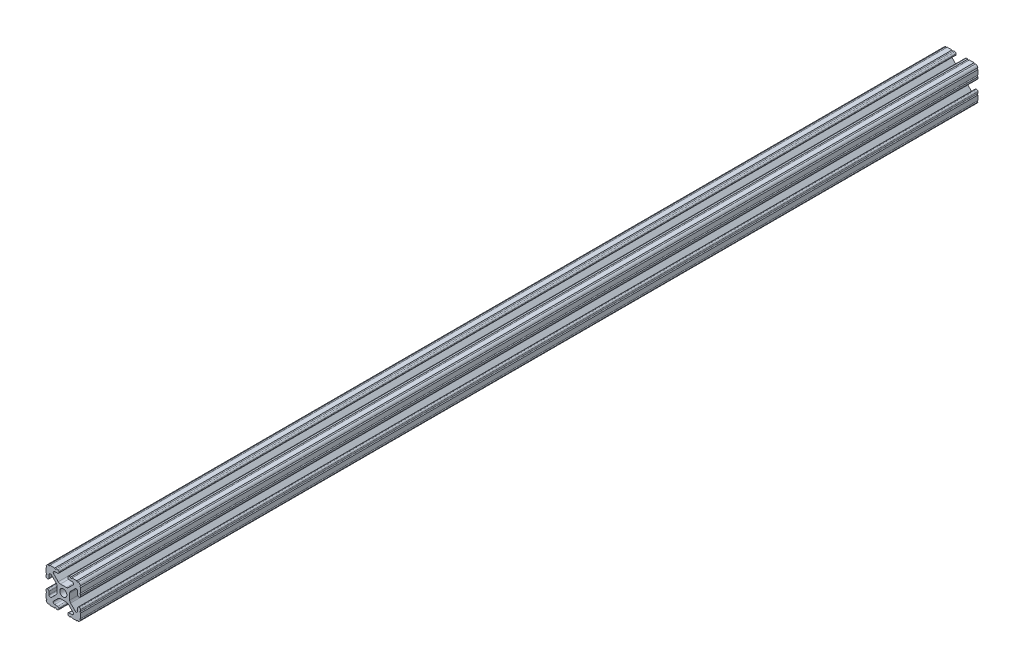
SolidWorks part; units mm, degrees
material "6061-T6 (SS)"
ref_plane "Front Plane" through (0, 0, 0) normal (0, 0, 1) x (1, 0, 0)
ref_plane "Top Plane" through (0, 0, 0) normal (0, 1, 0) x (1, 0, 0)
ref_plane "Right Plane" through (0, 0, 0) normal (1, 0, 0) x (0, 0, -1)
sketch "Sketch2" plane through (0, 0, 0) normal (0, 0, 1) x (1, 0, 0)
  line L0 (0, 12.7) -> (0, -12.7) construction
  line L1 (-12.7, 0) -> (12.7, 0) construction
  line L2 (3.2512, -12.7) -> (12.7, -12.7)
  line L3 (12.7, -12.7) -> (12.7, -3.2512)
  line L4 (3.2512, -12.7) -> (3.2512, -10.4902)
  line L5 (3.2512, -10.4902) -> (8.9276, -10.4902)
  line L6 (8.9276, -10.4902) -> (3.0856, -4.6482)
  line L7 (0, 0) -> (12.7, -12.7) construction
  line L8 (12.7, -3.2512) -> (10.4902, -3.2512)
  line L9 (10.4902, -3.2512) -> (10.4902, -8.9276)
  line L10 (10.4902, -8.9276) -> (4.6482, -3.0856)
  circle A0 centre (0, 0) radius 2.6035
  arc A1 (6.3485, -10.4902) -> (7.1039, -8.6665) centre (6.3485, -9.4219) ccw construction
  point P8 (0, -4.6482)
  dimension "Center Hole Diameter" = 5.207
  dimension "Rail Height" = 25.4
  dimension "Rail Width" = 25.4
  dimension "T-Slot Width" = 6.5024
  dimension "Slot Inner Width" = 14.8336
  dimension "Thickness" = 2.2098
  dimension "Slot Depth" = 5.842
  dimension "D1" = 2.2098
sketch "Sketch3" plane through (0, 0, 0) normal (1, 0, 0) x (0, 0, -1)
  line L0 (-328.6125, -12.7) -> (328.6125, -12.7) construction
  line L1 (-303.2125, 0) -> (303.2125, 0) construction
  dimension "Length" = 657.225
  dimension "D1" = 25.4
sketch "Sketch4" plane through (0, 0, 0) normal (0, 0, 1) x (1, 0, 0)
  line L0 (4.1904, -12.7) -> (10.1173, -12.7)
  line L1 (3.2512, -12.7) -> (12.7, -12.7) construction
  line L2 (3.2512, -12.7) -> (3.2512, -10.4902) construction
  line L3 (3.2512, -10.4902) -> (8.9276, -10.4902) construction
  line L4 (3.2512, -11.4294) -> (3.2512, -11.7608)
  line L5 (4.1904, -10.4902) -> (6.3485, -10.4902)
  line L6 (0, -4.6482) -> (2.164, -4.6482)
  line L7 (8.9276, -10.4902) -> (3.0856, -4.6482) construction
  line L8 (3.7373, -5.2999) -> (7.1039, -8.6665)
  line L9 (12.7, -12.7) -> (12.7, -3.2512) construction
  line L10 (10.4902, -8.9276) -> (4.6482, -3.0856) construction
  line L11 (10.4902, -3.2512) -> (10.4902, -8.9276) construction
  line L12 (10.4902, -6.3485) -> (10.4902, -4.1904)
  line L13 (12.7, -3.2512) -> (10.4902, -3.2512) construction
  line L14 (11.4294, -3.2512) -> (11.7608, -3.2512)
  line L15 (12.7, -4.1904) -> (12.7, -10.1173)
  line L16 (8.6665, -7.1039) -> (5.2999, -3.7373)
  line L17 (4.6482, 0) -> (4.6482, -2.164)
  line L18 (-12.7, 0) -> (12.7, 0) construction
  line L19 (0, -4.6482) -> (0, -2.6035)
  line L20 (0, 12.7) -> (0, -12.7) construction
  line L21 (4.6482, 0) -> (2.6035, 0)
  arc A0 (3.2512, -11.7608) -> (4.1904, -12.7) centre (4.1904, -11.7608) ccw
  arc A2 (3.2512, -11.4294) -> (4.1904, -10.4902) centre (4.1904, -11.4294) cw
  arc A3 (6.3485, -10.4902) -> (7.1039, -8.6665) centre (6.3485, -9.4219) ccw
  arc A4 (2.164, -4.6482) -> (3.7373, -5.2999) centre (2.164, -6.8732) cw
  arc A5 (10.1173, -12.7) -> (12.7, -10.1173) centre (10.1173, -10.1173) ccw
  arc A6 (8.6665, -7.1039) -> (10.4902, -6.3485) centre (9.4219, -6.3485) ccw
  arc A7 (10.4902, -4.1904) -> (11.4294, -3.2512) centre (11.4294, -4.1904) cw
  arc A8 (11.7608, -3.2512) -> (12.7, -4.1904) centre (11.7608, -4.1904) cw
  arc A9 (5.2999, -3.7373) -> (4.6482, -2.164) centre (6.8732, -2.164) cw
  circle A10 centre (0, 0) radius 2.6035 construction
  arc A11 (0, -2.6035) -> (2.6035, 0) centre (0, 0) ccw
  dimension "D1" = 2.5827
  dimension "D2" = 2.225
  dimension "D3" = 0.9392
extrude "Boss-Extrude1" add sketch "Sketch4" along normal mid plane 657.225
sketch "Sketch5" plane through (0, 0, 0) normal (0, 0, 1) x (1, 0, 0)
  line L0 (3.2512, -12.7) -> (12.7, -12.7) construction
  line L1 (4.1904, -10.4902) -> (6.3485, -10.4902) construction
  line L3 (0, 0) -> (12.7, -12.7) construction
  line L4 (6.3485, -10.4902) -> (6.3485, -12.7) construction
  line L5 (8.9276, -10.4902) -> (3.0856, -4.6482) construction
  circle A0 centre (10.3562, -12.7) radius 0.5524
  circle A1 centre (5.796, -12.7) radius 0.5524
  circle A2 centre (12.7, -10.3562) radius 0.5524
  circle A3 centre (12.7, -5.796) radius 0.5524
  point P10 (5.2694, -10.4902)
  point P12 (9.4219, -6.3485)
  dimension "D1" = 1.1049
extrude "Cut-Extrude1" cut sketch "Sketch5" against normal through all both and the other way through all
mirror "Mirror1" about plane through (0, 0, 0) normal (1, 0, 0) of bodies 137 134
mirror "Mirror2" about plane through (0, 0, 0) normal (0, 1, 0) of bodies 135
equation "\"D1@Boss-Extrude1\"=\"Length@Sketch3\""
equation "\"D1@Sketch2\"=\"Thickness@Sketch2\""
equation "\"D2@Sketch4\"=\"Slot Inner Width@Sketch2\"*0.15"
equation "\"D1@Sketch4\"=\"D3@Sketch4\"*2.75"
equation "\"D3@Sketch4\"=\"Thickness@Sketch2\"*0.425"
equation "\"D1@Sketch5\"=\"Thickness@Sketch2\"*0.5"
equation "\"TinesBase\"=28"
equation "\"TinesBaseOML\"=25.875"
equation "\"Length@Sketch3\"=\"TinesBaseOML\""
